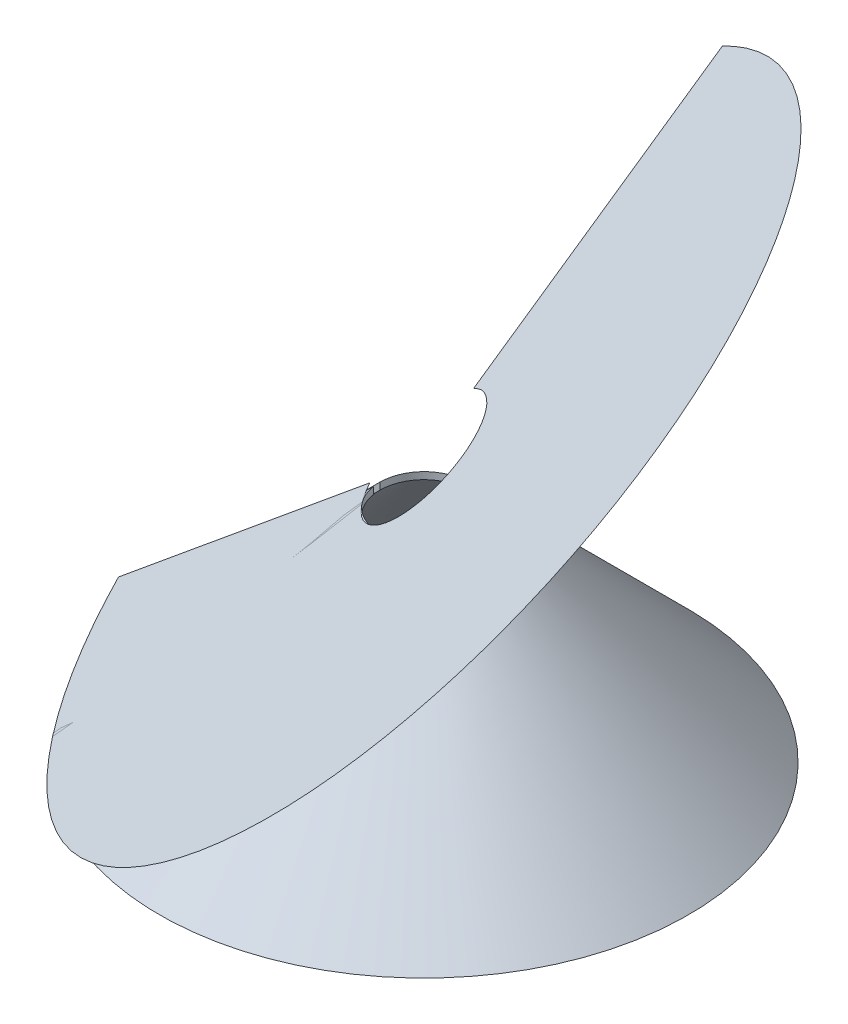
SolidWorks part; units mm, degrees
ref_plane "Front Plane" through (0, 0, 0) normal (0, 0, 1) x (1, 0, 0)
ref_plane "Top Plane" through (0, 0, 0) normal (0, 1, 0) x (1, 0, 0)
ref_plane "Right Plane" through (0, 0, 0) normal (1, 0, 0) x (0, 0, -1)
sketch "Sketch1" plane through (0, 0, 0) normal (0, 0, 1) x (1, 0, 0)
  line L0 (0, 0) -> (0, 38)
  line L1 (0, 38) -> (38, 0)
  line L2 (38, 0) -> (0, 0)
revolve "Revolve1" add sketch "Sketch1" angle 360 about L0
sketch "Sketch2" plane through (0, 0, 0) normal (0, 0, 1) x (1, 0, 0)
  line L0 (0, 0) -> (0, 37)
  line L1 (0, 37) -> (37, 0)
  line L2 (37, 0) -> (0, 0)
revolve "Cut-Revolve1" cut sketch "Sketch2" angle 360 about L0
sketch "Sketch3" plane through (0, 0, 0) normal (1, 0, 0) x (0, 0, -1)
  line L0 (0, 0) -> (0, 42.8971)
  line L1 (-38, 0) -> (38, 0) construction
  line L2 (0, 42.8971) -> (6.35, 42.8971)
  line L3 (6.35, 42.8971) -> (6.35, 25.6031)
  line L4 (6.35, 25.6031) -> (0, 25.6031)
  line L5 (0, 25.6031) -> (0, 42.8971)
revolve "Cut-Revolve2" cut sketch "Sketch3" angle 360 about L0
sketch "Sketch4" plane through (0, 0, 0) normal (0, 0, 1) x (1, 0, 0)
  line L0 (0, 31.65) -> (0, 0)
  line L1 (6.35, 31.65) -> (-6.35, 31.65) construction
sketch "Sketch15" plane through (0, 0, 0) normal (0, 0, 1) x (1, 0, 0)
  line L0 (-39.6189, 0.7344) -> (-37.9288, -0.9557)
  line L1 (-37.9288, -0.9557) -> (-4.0877, 32.8854)
  line L2 (-4.0877, 32.8854) -> (-5.7778, 34.5755)
  line L3 (-5.7778, 34.5755) -> (-39.6189, 0.7344)
extrude "Cut-Extrude1" cut sketch "Sketch15" along normal blind 1 contours L3 L0 L1 L2
surface "Surface-Flatten1"
